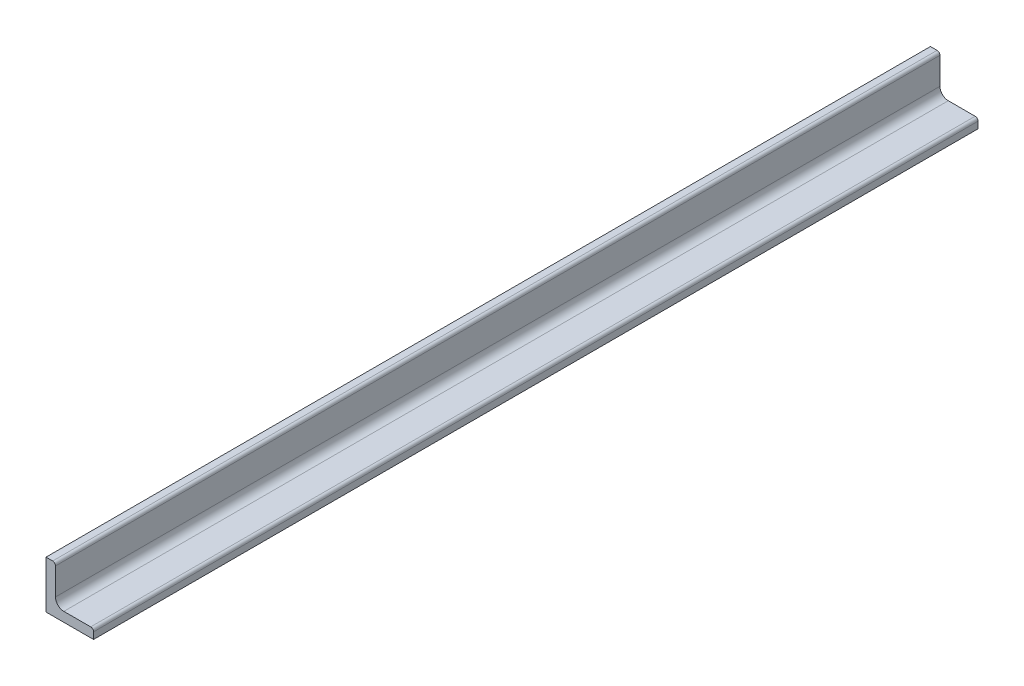
SolidWorks part; units mm, degrees
ref_plane "Спереди" through (0, 0, 0) normal (0, 0, 1) x (1, 0, 0)
ref_plane "Сверху" through (0, 0, 0) normal (0, 1, 0) x (1, 0, 0)
ref_plane "Справа" through (0, 0, 0) normal (1, 0, 0) x (0, 0, -1)
sketch "Эскиз1" plane through (0, 0, 0) normal (0, 0, 1) x (1, 0, 0)
  line L0 (-7.5, 12.5) -> (-7.5, -7.5)
  line L1 (-7.5, -7.5) -> (12.5, -7.5)
  line L2 (12.5, -7.5) -> (12.5, -4.7)
  line L3 (11.3, -3.5) -> (0, -3.5)
  line L4 (-3.5, 0) -> (-3.5, 11.3)
  line L5 (-4.7, 12.5) -> (-7.5, 12.5)
  arc A0 (-3.5, 0) -> (0, -3.5) centre (0, 0) ccw
  arc A1 (-3.5, 11.3) -> (-4.7, 12.5) centre (-4.7, 11.3) ccw
  arc A2 (12.5, -4.7) -> (11.3, -3.5) centre (11.3, -4.7) ccw
  dimension "D1" = 3.5
  dimension "D2" = 1.2
  dimension "D3" = 1.2
  dimension "D4" = 4
  dimension "D5" = 20
extrude "Бобышка-Вытянуть1" add sketch "Эскиз1" along normal blind 372
